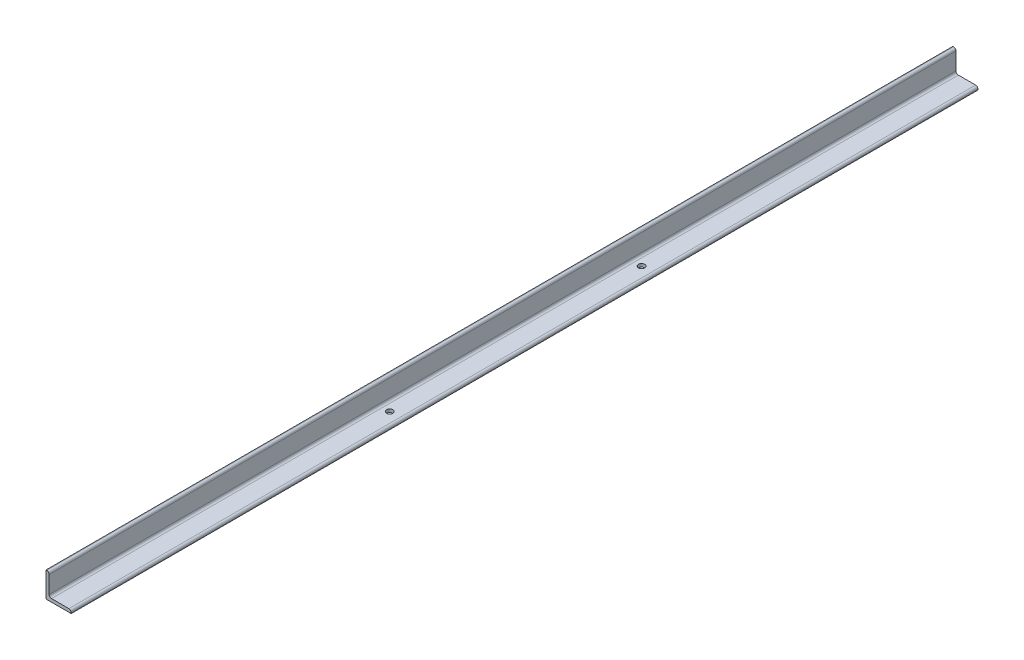
SolidWorks part; units mm, degrees
ref_plane "Front Plane" through (0, 0, 0) normal (0, 0, 1) x (1, 0, 0)
ref_plane "Top Plane" through (0, 0, 0) normal (0, 1, 0) x (1, 0, 0)
ref_plane "Right Plane" through (0, 0, 0) normal (1, 0, 0) x (0, 0, -1)
sketch "Sketch1" plane through (0, 0, 0) normal (0, 0, 1) x (1, 0, 0)
  line L0 (0, 0) -> (0, 50.8)
  line L1 (0, 50.8) -> (1.5926, 50.8)
  line L2 (6.35, 46.0426) -> (6.35, 11.1125)
  line L3 (11.1125, 6.35) -> (46.0426, 6.35)
  line L4 (50.8, 1.5926) -> (50.8, 0)
  line L5 (50.8, 0) -> (0, 0)
  arc A0 (50.8, 1.5926) -> (46.0426, 6.35) centre (46.0426, 1.5926) ccw
  arc A1 (1.5926, 50.8) -> (6.35, 46.0426) centre (1.5926, 46.0426) cw
  arc A2 (11.1125, 6.35) -> (6.35, 11.1125) centre (11.1125, 11.1125) cw
  circle A3 centre (0, 0) radius 4.7625 construction
  dimension "D2" = 1.5926
  dimension "Radius_1" = 4.7625
  dimension "Radius_2" = 4.7625
  dimension "D1" = 6.35
  dimension "V_leg" = 50.8
  dimension "H_leg" = 50.8
  dimension "Thickness" = 6.35
  dimension "Flat_wid" = 1.5926
extrude "Boss-Extrude1" add sketch "Sketch1" along normal mid plane 1828.8
sketch "Sketch5" plane through (0, 0, 0) normal (0, -1, 0) x (1, 0, 0)
  line L3 (25.4, -914.4) -> (25.4, 914.4) construction
  line L6 (0, 0) -> (50.8, 0) construction
  line L7 (50.8, 914.4) -> (50.8, -914.4) construction
  line L11 (0, -914.4) -> (50.8, -914.4) construction
  line L12 (0, 914.4) -> (50.8, 914.4) construction
  circle A0 centre (25.4, -261.366) radius 6.35
  circle A1 centre (25.4, 246.634) radius 6.35
  dimension "D1" = 653.034
  dimension "D2" = 667.766
extrude "Cut-Extrude2" cut sketch "Sketch5" against normal up to next
